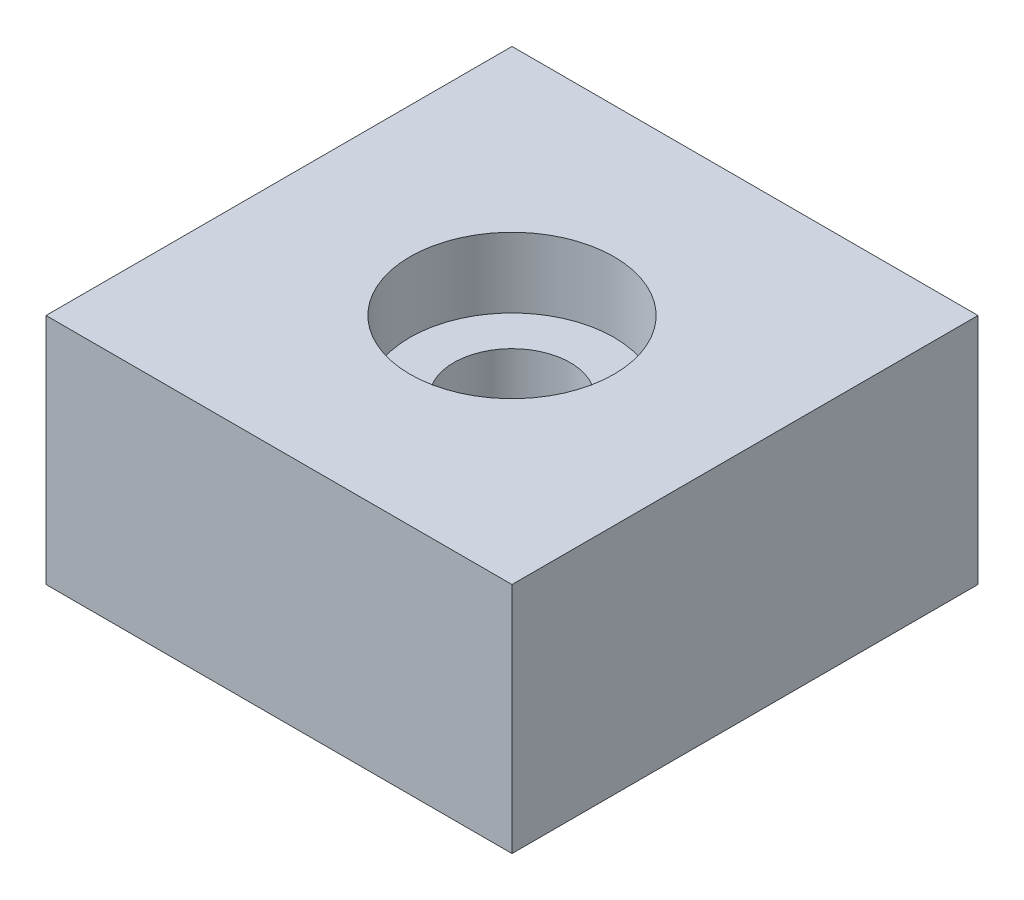
SolidWorks part; units mm, degrees
ref_plane "Front Plane" through (0, 0, 0) normal (0, 0, 1) x (1, 0, 0)
ref_plane "Top Plane" through (0, 0, 0) normal (0, 1, 0) x (1, 0, 0)
ref_plane "Right Plane" through (0, 0, 0) normal (1, 0, 0) x (0, 0, -1)
sketch "Sketch2" plane through (0, 0, 0) normal (0, 1, 0) x (1, 0, 0)
  line L1 (-25.4, -25.4) -> (25.4, -25.4)
  line L2 (-25.4, -25.4) -> (-25.4, 25.4)
  line L3 (-25.4, 25.4) -> (25.4, 25.4)
  line L4 (25.4, -25.4) -> (25.4, 25.4)
  line L5 (-25.4, -25.4) -> (25.4, 25.4) construction
  line L6 (-25.4, 25.4) -> (25.4, -25.4) construction
  point P0 (0, 0)
  dimension "D1" = 50.8
  dimension "D2" = 50.8
extrude "Boss-Extrude1" add sketch "Sketch2" along normal blind 25.4
hole_wizard "CBORE for #00 Binding Head Machine Screw1" positions "Sketch3" profile "Sketch4" counterbore size "#00" standard "ANSI Inch" end condition through all
sketch "Sketch3" plane through (0, 25.4, 0) normal (0, 1, 0) x (1, 0, 0)
  line L0 (-25.4, 25.4) -> (-25.4, -25.4) construction
  line L2 (-25.4, -25.4) -> (25.4, -25.4) construction
  point P0 (0, 0)
  dimension "D1" = 25.4
  dimension "D2" = 25.4
sketch "Sketch4" plane through (0, 25.4, 0) normal (1, 0, 0) x (0, 0, 1)
  line L0 (0, 0) -> (0, 25.4)
  line L1 (0, 25.4) -> (6.35, 25.4)
  line L3 (6.35, 25.4) -> (6.35, 7.62)
  line L4 (6.35, 7.62) -> (11.1125, 7.62)
  line L5 (11.1125, 7.62) -> (11.1125, 0)
  line L7 (11.1125, 0) -> (0, 0)
  line L11 (0, -6.35) -> (0, 107.95) construction
  dimension "Thru Hole Dia." = 12.7
  dimension "Thru Hole Depth" = 25.4
  dimension "C'Bore Dia." = 22.225
  dimension "C'Bore Depth" = 7.62
